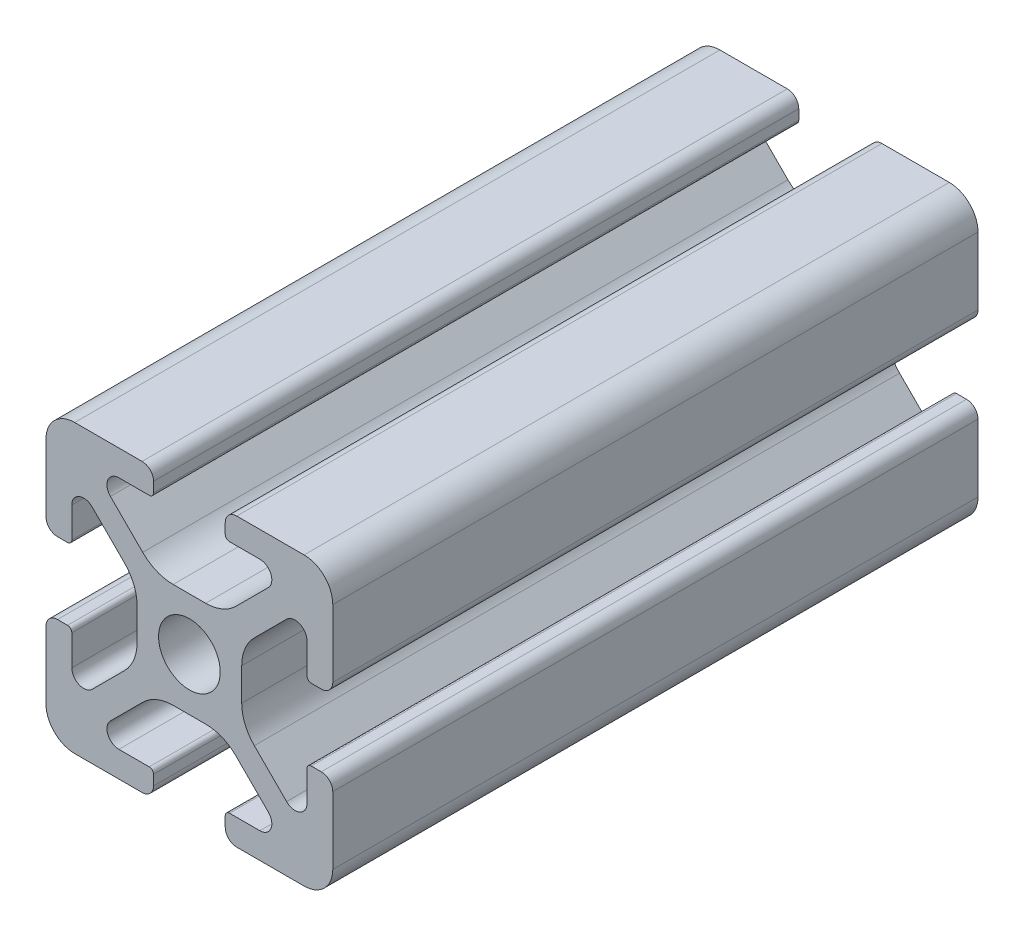
SolidWorks part; units mm, degrees
ref_plane "Front" through (0, 0, 0) normal (0, 0, 1) x (1, 0, 0)
ref_plane "Top" through (0, 0, 0) normal (0, 1, 0) x (1, 0, 0)
ref_plane "Right" through (0, 0, 0) normal (1, 0, 0) x (0, 0, -1)
sketch "Support-Front" plane through (0, 0, 0) normal (0, 0, 1) x (1, 0, 0)
  line L0 (10, 0) -> (-10, 0) construction
  line L1 (-10, -10) -> (10, -10)
  line L2 (-10, -10) -> (-10, 10)
  line L3 (-10, 10) -> (10, 10)
  line L4 (10, -10) -> (10, 10)
  line L5 (0, 10) -> (0, -10) construction
  dimension "Height-Profile" = 20
  dimension "Width-Profile" = 20
sketch "Support-Right-Length" plane through (0, 0, 0) normal (1, 0, 0) x (0, 0, -1)
  line L0 (0, -10) -> (0, 10) construction
  line L1 (-25, 10) -> (25, 10)
  line L2 (-25, 10) -> (-25, -10)
  line L3 (-25, -10) -> (25, -10)
  line L4 (25, 10) -> (25, -10)
  dimension "Length-Profile" = 50
sketch "Support-Profile" plane through (0, 0, 0) normal (0, 0, 1) x (1, 0, 0)
  line L8 (4.9176, -8.2) -> (2.8, -8.2)
  line L9 (2.5, -8.5) -> (2.5, -9.2)
  line L10 (3.3, -10) -> (8, -10)
  line L11 (10, -8) -> (10, -3.3)
  line L24 (9.2, -2.5) -> (8.5, -2.5)
  line L25 (8.2, -2.8) -> (8.2, -4.9176)
  line L26 (6.779, -5.5062) -> (4.5287, -3.2559)
  line L27 (3.65, -1.1346) -> (3.65, 1.1346)
  line L28 (4.5287, 3.2559) -> (6.779, 5.5062)
  line L29 (8.2, 4.9176) -> (8.2, 2.8)
  line L30 (8.5, 2.5) -> (9.2, 2.5)
  line L31 (10, 3.3) -> (10, 8)
  line L32 (8, 10) -> (3.3, 10)
  line L33 (2.5, 9.2) -> (2.5, 8.5)
  line L34 (2.8, 8.2) -> (4.9176, 8.2)
  line L35 (5.5062, 6.779) -> (3.2559, 4.5287)
  line L40 (1.1346, 3.65) -> (-1.1346, 3.65)
  line L41 (-3.2559, 4.5287) -> (-5.5062, 6.779)
  line L42 (-4.9176, 8.2) -> (-2.8, 8.2)
  line L43 (-2.5, 8.5) -> (-2.5, 9.2)
  line L44 (-3.3, 10) -> (-8, 10)
  line L45 (-10, 8) -> (-10, 3.3)
  line L46 (-9.2, 2.5) -> (-8.5, 2.5)
  line L47 (-8.2, 2.8) -> (-8.2, 4.9176)
  line L48 (-6.779, 5.5062) -> (-4.5287, 3.2559)
  line L49 (-3.65, 1.1346) -> (-3.65, -1.1346)
  line L50 (-4.5287, -3.2559) -> (-6.779, -5.5062)
  line L51 (-8.2, -4.9176) -> (-8.2, -2.8)
  line L52 (-8.5, -2.5) -> (-9.2, -2.5)
  line L53 (-10, -3.3) -> (-10, -8)
  line L54 (-8, -10) -> (-3.3, -10)
  line L55 (-2.5, -9.2) -> (-2.5, -8.5)
  line L56 (-2.8, -8.2) -> (-4.9176, -8.2)
  line L57 (-5.5062, -6.779) -> (-3.2559, -4.5287)
  line L58 (-1.1346, -3.65) -> (1.1346, -3.65)
  line L59 (3.2559, -4.5287) -> (5.5062, -6.779)
  circle A2 centre (0, 0) radius 2.15
  arc A3 (2.8, -8.2) -> (2.5, -8.5) centre (2.8, -8.5) ccw
  arc A5 (2.5, -9.2) -> (3.3, -10) centre (3.3, -9.2) ccw
  arc A24 (8, -10) -> (10, -8) centre (8, -8) ccw
  arc A25 (10, -3.3) -> (9.2, -2.5) centre (9.2, -3.3) ccw
  arc A26 (8.5, -2.5) -> (8.2, -2.8) centre (8.5, -2.8) ccw
  arc A27 (6.779, -5.5062) -> (8.2, -4.9176) centre (7.3676, -4.9176) ccw
  arc A28 (3.65, -1.1346) -> (4.5287, -3.2559) centre (6.65, -1.1346) ccw
  arc A29 (4.5287, 3.2559) -> (3.65, 1.1346) centre (6.65, 1.1346) ccw
  arc A30 (8.2, 4.9176) -> (6.779, 5.5062) centre (7.3676, 4.9176) ccw
  arc A31 (8.2, 2.8) -> (8.5, 2.5) centre (8.5, 2.8) ccw
  arc A32 (9.2, 2.5) -> (10, 3.3) centre (9.2, 3.3) ccw
  arc A33 (10, 8) -> (8, 10) centre (8, 8) ccw
  arc A34 (3.3, 10) -> (2.5, 9.2) centre (3.3, 9.2) ccw
  arc A35 (2.5, 8.5) -> (2.8, 8.2) centre (2.8, 8.5) ccw
  arc A38 (5.5062, 6.779) -> (4.9176, 8.2) centre (4.9176, 7.3676) ccw
  arc A39 (1.1346, 3.65) -> (3.2559, 4.5287) centre (1.1346, 6.65) ccw
  arc A44 (-3.2559, 4.5287) -> (-1.1346, 3.65) centre (-1.1346, 6.65) ccw
  arc A45 (-4.9176, 8.2) -> (-5.5062, 6.779) centre (-4.9176, 7.3676) ccw
  arc A46 (-2.8, 8.2) -> (-2.5, 8.5) centre (-2.8, 8.5) ccw
  arc A47 (-2.5, 9.2) -> (-3.3, 10) centre (-3.3, 9.2) ccw
  arc A48 (-8, 10) -> (-10, 8) centre (-8, 8) ccw
  arc A49 (-10, 3.3) -> (-9.2, 2.5) centre (-9.2, 3.3) ccw
  arc A50 (-8.5, 2.5) -> (-8.2, 2.8) centre (-8.5, 2.8) ccw
  arc A51 (-6.779, 5.5062) -> (-8.2, 4.9176) centre (-7.3676, 4.9176) ccw
  arc A52 (-3.65, 1.1346) -> (-4.5287, 3.2559) centre (-6.65, 1.1346) ccw
  arc A53 (-4.5287, -3.2559) -> (-3.65, -1.1346) centre (-6.65, -1.1346) ccw
  arc A54 (-8.2, -4.9176) -> (-6.779, -5.5062) centre (-7.3676, -4.9176) ccw
  arc A55 (-8.2, -2.8) -> (-8.5, -2.5) centre (-8.5, -2.8) ccw
  arc A56 (-9.2, -2.5) -> (-10, -3.3) centre (-9.2, -3.3) ccw
  arc A57 (-10, -8) -> (-8, -10) centre (-8, -8) ccw
  arc A58 (-3.3, -10) -> (-2.5, -9.2) centre (-3.3, -9.2) ccw
  arc A59 (-2.5, -8.5) -> (-2.8, -8.2) centre (-2.8, -8.5) ccw
  arc A60 (-5.5062, -6.779) -> (-4.9176, -8.2) centre (-4.9176, -7.3676) ccw
  arc A61 (-1.1346, -3.65) -> (-3.2559, -4.5287) centre (-1.1346, -6.65) ccw
  arc A62 (3.2559, -4.5287) -> (1.1346, -3.65) centre (1.1346, -6.65) ccw
  arc A63 (4.9176, -8.2) -> (5.5062, -6.779) centre (4.9176, -7.3676) ccw
ref_plane "Ref-Plane-1" through (0, 0, 25) normal (0, 0, 1) x (1, 0, 0)
ref_plane "Ref-Plane-2" through (0, 0, -25) normal (0, 0, 1) x (1, 0, 0)
sketch "Sketch4" plane through (0, 0, 25) normal (0, 0, 1) x (1, 0, 0)
  line L0 (-10, -10) -> (-10, 10) construction
  line L1 (-10, -10) -> (10, -10) construction
  line L2 (10, -10) -> (10, 10) construction
  line L3 (-10, 10) -> (10, 10) construction
  line L4 (-10, -10) -> (-10, 10)
  line L5 (-10, -10) -> (10, -10)
  line L6 (10, -10) -> (10, 10)
  line L7 (-10, 10) -> (10, 10)
extrude "Body" add sketch "Sketch4" against normal blind 45
sketch "Sketch16" plane through (0, 0, 0) normal (0, 0, 1) x (1, 0, 0)
  line L40 (4.9176, -8.2) -> (2.8, -8.2)
  line L41 (2.5, -8.5) -> (2.5, -9.2)
  line L42 (3.3, -10) -> (8, -10)
  line L43 (10, -8) -> (10, -3.3)
  line L44 (9.2, -2.5) -> (8.5, -2.5)
  line L45 (8.2, -2.8) -> (8.2, -4.9176)
  line L46 (6.779, -5.5062) -> (4.5287, -3.2559)
  line L47 (3.65, -1.1346) -> (3.65, 1.1346)
  line L48 (4.5287, 3.2559) -> (6.779, 5.5062)
  line L49 (8.2, 4.9176) -> (8.2, 2.8)
  line L50 (8.5, 2.5) -> (9.2, 2.5)
  line L51 (10, 3.3) -> (10, 8)
  line L52 (8, 10) -> (3.3, 10)
  line L53 (2.5, 9.2) -> (2.5, 8.5)
  line L54 (2.8, 8.2) -> (4.9176, 8.2)
  line L55 (5.5062, 6.779) -> (3.2559, 4.5287)
  line L56 (1.1346, 3.65) -> (-1.1346, 3.65)
  line L57 (-3.2559, 4.5287) -> (-5.5062, 6.779)
  line L58 (-4.9176, 8.2) -> (-2.8, 8.2)
  line L59 (-2.5, 8.5) -> (-2.5, 9.2)
  line L60 (-3.3, 10) -> (-8, 10)
  line L61 (-10, 8) -> (-10, 3.3)
  line L62 (-9.2, 2.5) -> (-8.5, 2.5)
  line L63 (-8.2, 2.8) -> (-8.2, 4.9176)
  line L64 (-6.779, 5.5062) -> (-4.5287, 3.2559)
  line L65 (-3.65, 1.1346) -> (-3.65, -1.1346)
  line L66 (-4.5287, -3.2559) -> (-6.779, -5.5062)
  line L67 (-8.2, -4.9176) -> (-8.2, -2.8)
  line L68 (-8.5, -2.5) -> (-9.2, -2.5)
  line L69 (-10, -3.3) -> (-10, -8)
  line L70 (-8, -10) -> (-3.3, -10)
  line L71 (-2.5, -9.2) -> (-2.5, -8.5)
  line L72 (-2.8, -8.2) -> (-4.9176, -8.2)
  line L73 (-5.5062, -6.779) -> (-3.2559, -4.5287)
  line L74 (-1.1346, -3.65) -> (1.1346, -3.65)
  line L75 (3.2559, -4.5287) -> (5.5062, -6.779)
  line L76 (4.9176, -8.2) -> (2.8, -8.2)
  line L77 (2.5, -8.5) -> (2.5, -9.2)
  line L78 (3.3, -10) -> (8, -10)
  line L79 (10, -8) -> (10, -3.3)
  line L80 (9.2, -2.5) -> (8.5, -2.5)
  line L81 (8.2, -2.8) -> (8.2, -4.9176)
  line L82 (6.779, -5.5062) -> (4.5287, -3.2559)
  line L83 (3.65, -1.1346) -> (3.65, 1.1346)
  line L84 (4.5287, 3.2559) -> (6.779, 5.5062)
  line L85 (8.2, 4.9176) -> (8.2, 2.8)
  line L86 (8.5, 2.5) -> (9.2, 2.5)
  line L87 (10, 3.3) -> (10, 8)
  line L88 (8, 10) -> (3.3, 10)
  line L89 (2.5, 9.2) -> (2.5, 8.5)
  line L90 (2.8, 8.2) -> (4.9176, 8.2)
  line L91 (5.5062, 6.779) -> (3.2559, 4.5287)
  line L92 (1.1346, 3.65) -> (-1.1346, 3.65)
  line L93 (-3.2559, 4.5287) -> (-5.5062, 6.779)
  line L94 (-4.9176, 8.2) -> (-2.8, 8.2)
  line L95 (-2.5, 8.5) -> (-2.5, 9.2)
  line L96 (-3.3, 10) -> (-8, 10)
  line L97 (-10, 8) -> (-10, 3.3)
  line L98 (-9.2, 2.5) -> (-8.5, 2.5)
  line L99 (-8.2, 2.8) -> (-8.2, 4.9176)
  line L100 (-6.779, 5.5062) -> (-4.5287, 3.2559)
  line L101 (-3.65, 1.1346) -> (-3.65, -1.1346)
  line L102 (-4.5287, -3.2559) -> (-6.779, -5.5062)
  line L103 (-8.2, -4.9176) -> (-8.2, -2.8)
  line L104 (-8.5, -2.5) -> (-9.2, -2.5)
  line L105 (-10, -3.3) -> (-10, -8)
  line L106 (-8, -10) -> (-3.3, -10)
  line L107 (-2.5, -9.2) -> (-2.5, -8.5)
  line L108 (-2.8, -8.2) -> (-4.9176, -8.2)
  line L109 (-5.5062, -6.779) -> (-3.2559, -4.5287)
  line L110 (-1.1346, -3.65) -> (1.1346, -3.65)
  line L111 (3.2559, -4.5287) -> (5.5062, -6.779)
  circle A7 centre (0, 0) radius 2.15 construction
  circle A8 centre (0, 0) radius 2.15
  arc A43 (2.8, -8.2) -> (2.5, -8.5) centre (2.8, -8.5) ccw
  arc A44 (2.5, -9.2) -> (3.3, -10) centre (3.3, -9.2) ccw
  arc A45 (8, -10) -> (10, -8) centre (8, -8) ccw
  arc A46 (10, -3.3) -> (9.2, -2.5) centre (9.2, -3.3) ccw
  arc A47 (8.5, -2.5) -> (8.2, -2.8) centre (8.5, -2.8) ccw
  arc A48 (6.779, -5.5062) -> (8.2, -4.9176) centre (7.3676, -4.9176) ccw
  arc A49 (3.65, -1.1346) -> (4.5287, -3.2559) centre (6.65, -1.1346) ccw
  arc A50 (4.5287, 3.2559) -> (3.65, 1.1346) centre (6.65, 1.1346) ccw
  arc A51 (8.2, 4.9176) -> (6.779, 5.5062) centre (7.3676, 4.9176) ccw
  arc A52 (8.2, 2.8) -> (8.5, 2.5) centre (8.5, 2.8) ccw
  arc A53 (9.2, 2.5) -> (10, 3.3) centre (9.2, 3.3) ccw
  arc A54 (10, 8) -> (8, 10) centre (8, 8) ccw
  arc A55 (3.3, 10) -> (2.5, 9.2) centre (3.3, 9.2) ccw
  arc A56 (2.5, 8.5) -> (2.8, 8.2) centre (2.8, 8.5) ccw
  arc A57 (5.5062, 6.779) -> (4.9176, 8.2) centre (4.9176, 7.3676) ccw
  arc A58 (1.1346, 3.65) -> (3.2559, 4.5287) centre (1.1346, 6.65) ccw
  arc A59 (-3.2559, 4.5287) -> (-1.1346, 3.65) centre (-1.1346, 6.65) ccw
  arc A60 (-4.9176, 8.2) -> (-5.5062, 6.779) centre (-4.9176, 7.3676) ccw
  arc A61 (-2.8, 8.2) -> (-2.5, 8.5) centre (-2.8, 8.5) ccw
  arc A62 (-2.5, 9.2) -> (-3.3, 10) centre (-3.3, 9.2) ccw
  arc A63 (-8, 10) -> (-10, 8) centre (-8, 8) ccw
  arc A64 (-10, 3.3) -> (-9.2, 2.5) centre (-9.2, 3.3) ccw
  arc A65 (-8.5, 2.5) -> (-8.2, 2.8) centre (-8.5, 2.8) ccw
  arc A66 (-6.779, 5.5062) -> (-8.2, 4.9176) centre (-7.3676, 4.9176) ccw
  arc A67 (-3.65, 1.1346) -> (-4.5287, 3.2559) centre (-6.65, 1.1346) ccw
  arc A68 (-4.5287, -3.2559) -> (-3.65, -1.1346) centre (-6.65, -1.1346) ccw
  arc A69 (-8.2, -4.9176) -> (-6.779, -5.5062) centre (-7.3676, -4.9176) ccw
  arc A70 (-8.2, -2.8) -> (-8.5, -2.5) centre (-8.5, -2.8) ccw
  arc A71 (-9.2, -2.5) -> (-10, -3.3) centre (-9.2, -3.3) ccw
  arc A72 (-10, -8) -> (-8, -10) centre (-8, -8) ccw
  arc A73 (-3.3, -10) -> (-2.5, -9.2) centre (-3.3, -9.2) ccw
  arc A74 (-2.5, -8.5) -> (-2.8, -8.2) centre (-2.8, -8.5) ccw
  arc A75 (-5.5062, -6.779) -> (-4.9176, -8.2) centre (-4.9176, -7.3676) ccw
  arc A76 (-1.1346, -3.65) -> (-3.2559, -4.5287) centre (-1.1346, -6.65) ccw
  arc A77 (3.2559, -4.5287) -> (1.1346, -3.65) centre (1.1346, -6.65) ccw
  arc A78 (4.9176, -8.2) -> (5.5062, -6.779) centre (4.9176, -7.3676) ccw
  arc A79 (2.8, -8.2) -> (2.5, -8.5) centre (2.8, -8.5) ccw
  arc A80 (2.5, -9.2) -> (3.3, -10) centre (3.3, -9.2) ccw
  arc A81 (8, -10) -> (10, -8) centre (8, -8) ccw
  arc A82 (10, -3.3) -> (9.2, -2.5) centre (9.2, -3.3) ccw
  arc A83 (8.5, -2.5) -> (8.2, -2.8) centre (8.5, -2.8) ccw
  arc A84 (6.779, -5.5062) -> (8.2, -4.9176) centre (7.3676, -4.9176) ccw
  arc A85 (3.65, -1.1346) -> (4.5287, -3.2559) centre (6.65, -1.1346) ccw
  arc A86 (4.5287, 3.2559) -> (3.65, 1.1346) centre (6.65, 1.1346) ccw
  arc A87 (8.2, 4.9176) -> (6.779, 5.5062) centre (7.3676, 4.9176) ccw
  arc A88 (8.2, 2.8) -> (8.5, 2.5) centre (8.5, 2.8) ccw
  arc A89 (9.2, 2.5) -> (10, 3.3) centre (9.2, 3.3) ccw
  arc A90 (10, 8) -> (8, 10) centre (8, 8) ccw
  arc A91 (3.3, 10) -> (2.5, 9.2) centre (3.3, 9.2) ccw
  arc A92 (2.5, 8.5) -> (2.8, 8.2) centre (2.8, 8.5) ccw
  arc A93 (5.5062, 6.779) -> (4.9176, 8.2) centre (4.9176, 7.3676) ccw
  arc A94 (1.1346, 3.65) -> (3.2559, 4.5287) centre (1.1346, 6.65) ccw
  arc A95 (-3.2559, 4.5287) -> (-1.1346, 3.65) centre (-1.1346, 6.65) ccw
  arc A96 (-4.9176, 8.2) -> (-5.5062, 6.779) centre (-4.9176, 7.3676) ccw
  arc A97 (-2.8, 8.2) -> (-2.5, 8.5) centre (-2.8, 8.5) ccw
  arc A98 (-2.5, 9.2) -> (-3.3, 10) centre (-3.3, 9.2) ccw
  arc A99 (-8, 10) -> (-10, 8) centre (-8, 8) ccw
  arc A100 (-10, 3.3) -> (-9.2, 2.5) centre (-9.2, 3.3) ccw
  arc A101 (-8.5, 2.5) -> (-8.2, 2.8) centre (-8.5, 2.8) ccw
  arc A102 (-6.779, 5.5062) -> (-8.2, 4.9176) centre (-7.3676, 4.9176) ccw
  arc A103 (-3.65, 1.1346) -> (-4.5287, 3.2559) centre (-6.65, 1.1346) ccw
  arc A104 (-4.5287, -3.2559) -> (-3.65, -1.1346) centre (-6.65, -1.1346) ccw
  arc A105 (-8.2, -4.9176) -> (-6.779, -5.5062) centre (-7.3676, -4.9176) ccw
  arc A106 (-8.2, -2.8) -> (-8.5, -2.5) centre (-8.5, -2.8) ccw
  arc A107 (-9.2, -2.5) -> (-10, -3.3) centre (-9.2, -3.3) ccw
  arc A108 (-10, -8) -> (-8, -10) centre (-8, -8) ccw
  arc A109 (-3.3, -10) -> (-2.5, -9.2) centre (-3.3, -9.2) ccw
  arc A110 (-2.5, -8.5) -> (-2.8, -8.2) centre (-2.8, -8.5) ccw
  arc A111 (-5.5062, -6.779) -> (-4.9176, -8.2) centre (-4.9176, -7.3676) ccw
  arc A112 (-1.1346, -3.65) -> (-3.2559, -4.5287) centre (-1.1346, -6.65) ccw
  arc A113 (3.2559, -4.5287) -> (1.1346, -3.65) centre (1.1346, -6.65) ccw
  arc A114 (4.9176, -8.2) -> (5.5062, -6.779) centre (4.9176, -7.3676) ccw
  dimension "D1" = 0
extrude "Cut-Profile" cut sketch "Sketch16" against normal through all and the other way through all flip side to cut
